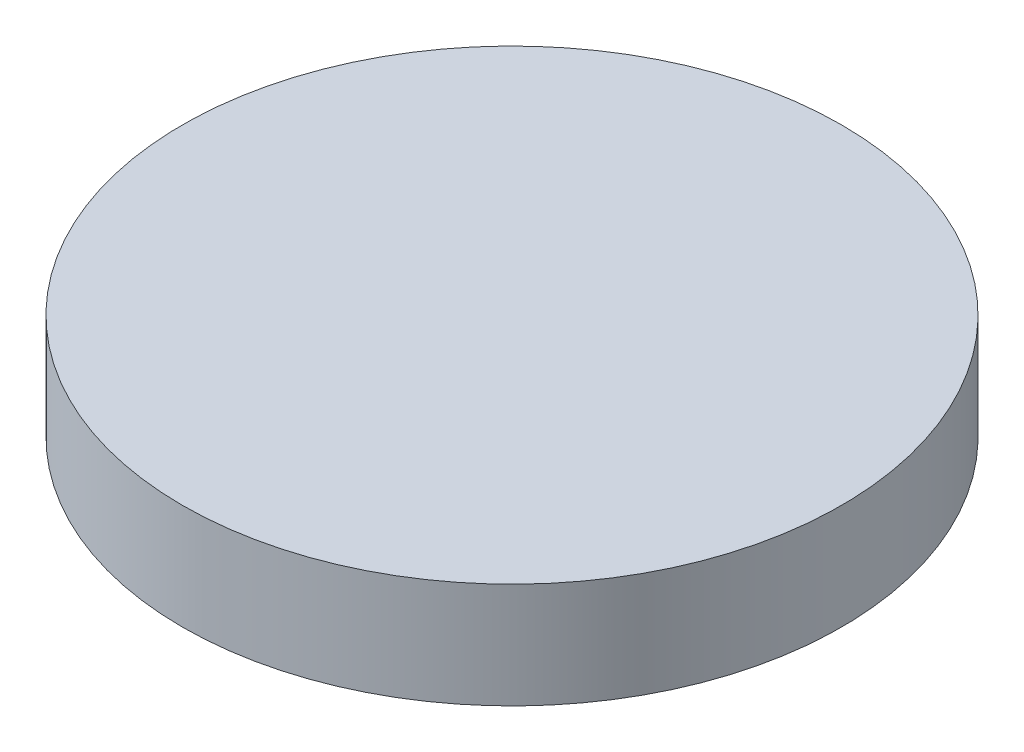
SolidWorks part; units mm, degrees
ref_plane "前视基准面" through (0, 0, 0) normal (0, 0, 1) x (1, 0, 0)
ref_plane "上视基准面" through (0, 0, 0) normal (0, 1, 0) x (1, 0, 0)
ref_plane "右视基准面" through (0, 0, 0) normal (1, 0, 0) x (0, 0, -1)
sketch "草图1" plane through (0, 0, 0) normal (0, 1, 0) x (1, 0, 0)
  circle A0 centre (0, 0) radius 6.25
  dimension "D1" = 12.5
extrude "凸台-拉伸1" add sketch "草图1" along normal blind 2
